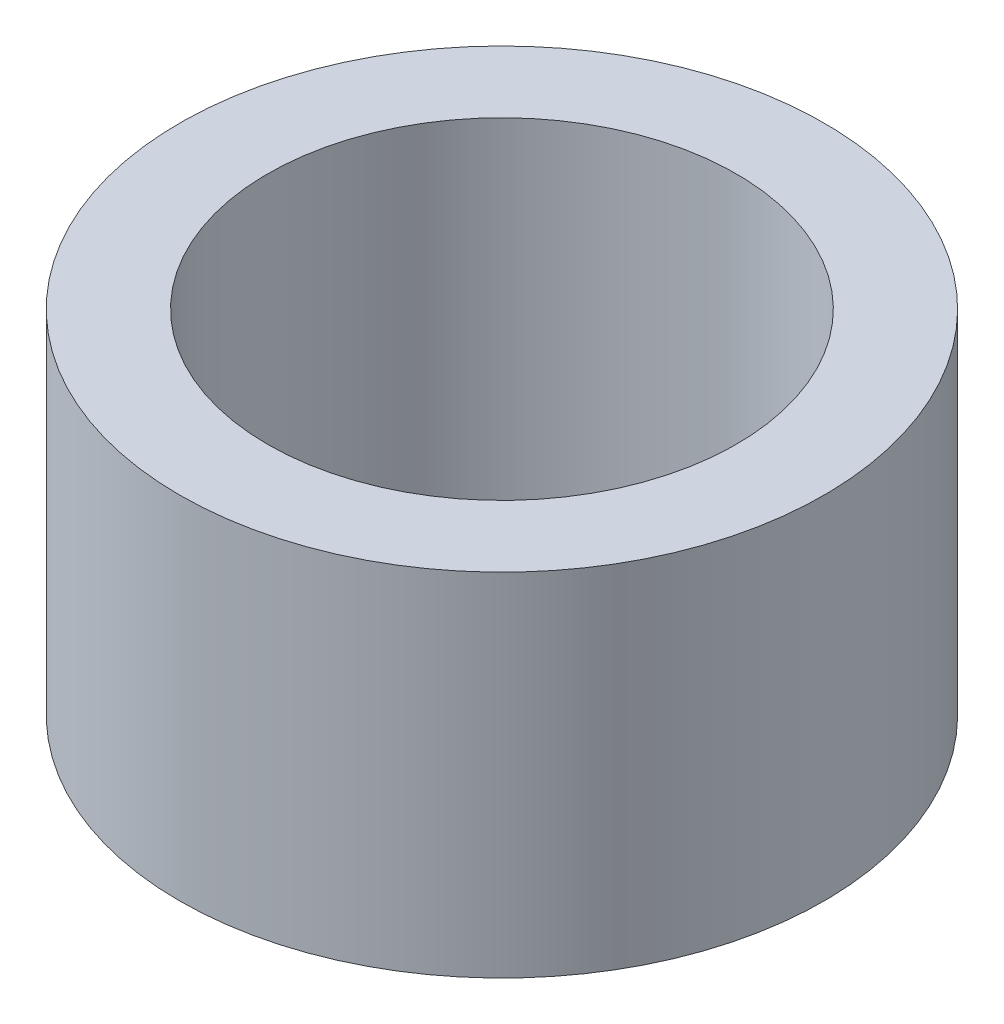
SolidWorks part; units mm, degrees
ref_plane "Front Plane" through (0, 0, 0) normal (0, 0, 1) x (1, 0, 0)
ref_plane "Top Plane" through (0, 0, 0) normal (0, 1, 0) x (1, 0, 0)
ref_plane "Right Plane" through (0, 0, 0) normal (1, 0, 0) x (0, 0, -1)
sketch "Sketch1" plane through (0, 0, 0) normal (0, 1, 0) x (1, 0, 0)
  circle A0 centre (0, 0) radius 2
  circle A1 centre (0, 0) radius 2.75
  dimension "D1" = 4
  dimension "D2" = 5.5
extrude "Boss-Extrude1" add sketch "Sketch1" along normal blind 3
